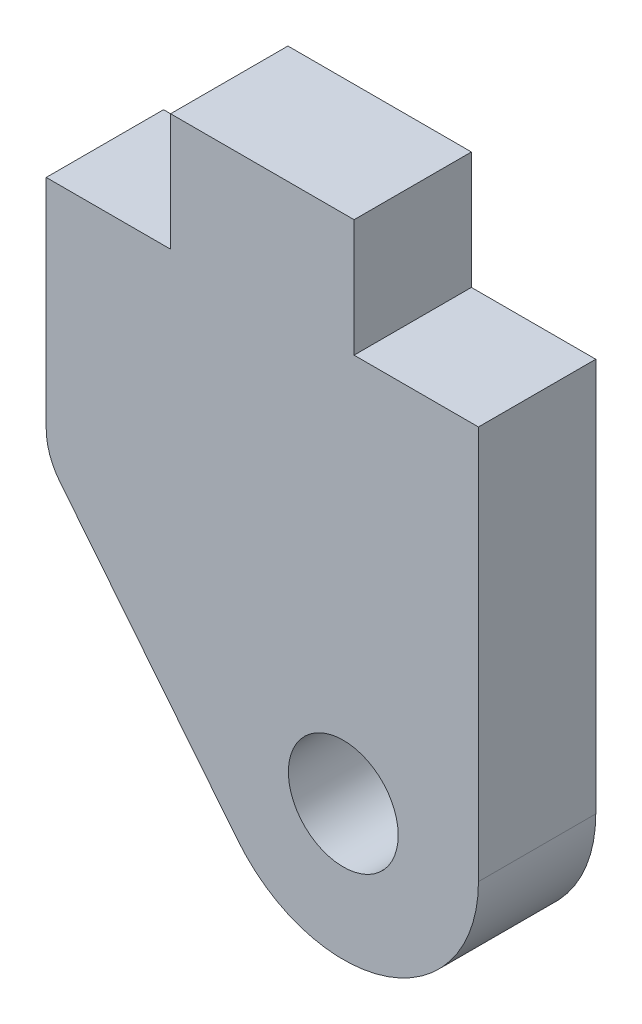
SolidWorks part; units mm, degrees
ref_plane "Front" through (0, 0, 0) normal (0, 0, 1) x (1, 0, 0)
ref_plane "Top" through (0, 0, 0) normal (0, 1, 0) x (1, 0, 0)
ref_plane "Right" through (0, 0, 0) normal (1, 0, 0) x (0, 0, -1)
sketch "Sketch1" plane through (0, 0, 0) normal (0, 0, 1) x (1, 0, 0)
  line L0 (-5.4762, -1.3818) -> (-0.6609, -7.3768)
  line L1 (5.8484, -5.0863) -> (5.8483, 5.569)
  line L2 (5.8483, 5.569) -> (2.4828, 5.569)
  line L3 (2.4828, 5.569) -> (2.4828, 8.744)
  line L4 (2.4828, 8.744) -> (-2.4829, 8.744)
  line L5 (-2.4829, 8.744) -> (-2.4829, 5.569)
  line L6 (-2.4829, 5.569) -> (-5.8484, 5.569)
  line L7 (-5.8484, 5.569) -> (-5.8484, -0.324)
  arc A0 (-5.8484, -0.324) -> (-5.4762, -1.3818) centre (-4.1593, -0.324) ccw
  arc A1 (-0.6609, -7.3768) -> (5.8484, -5.0863) centre (2.1907, -5.0863) ccw
  circle A2 centre (2.1907, -5.0863) radius 1.4859
extrude "Boss-Extrude1" add sketch "Sketch1" along normal blind 3.175
